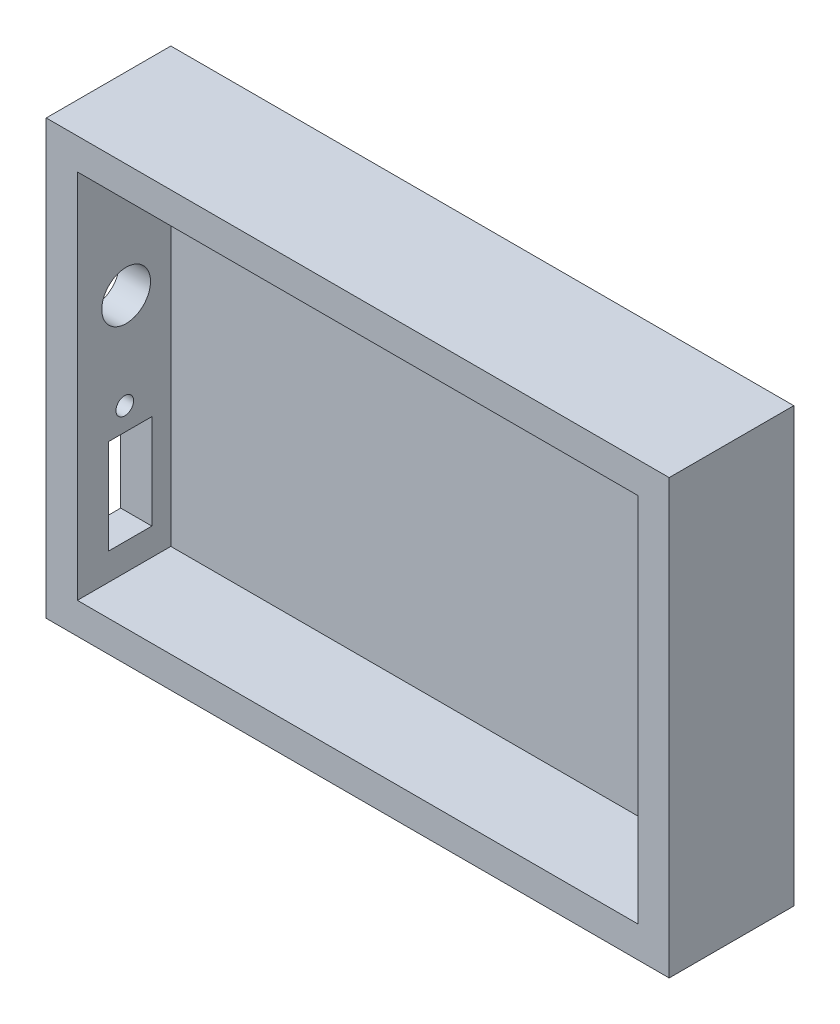
SolidWorks part; units mm, degrees
ref_plane "Front Plane" through (0, 0, 0) normal (0, 0, 1) x (1, 0, 0)
ref_plane "Top Plane" through (0, 0, 0) normal (0, 1, 0) x (1, 0, 0)
ref_plane "Right Plane" through (0, 0, 0) normal (1, 0, 0) x (0, 0, -1)
sketch "Sketch1" plane through (0, 0, 0) normal (0, 0, 1) x (1, 0, 0)
  line L1 (-115, 80) -> (115, 80)
  line L2 (-115, 80) -> (-115, -80)
  line L3 (-115, -80) -> (115, -80)
  line L4 (115, 80) -> (115, -80)
  line L5 (-115, 80) -> (115, -80) construction
  line L6 (-115, -80) -> (115, 80) construction
  point P0 (0, 0)
  dimension "D1" = 230
  dimension "D2" = 160
extrude "Boss-Extrude1" add sketch "Sketch1" along normal blind 46
shell "Shell1" thickness 11.5
sketch "Sketch2" plane through (-115, 0, 0) normal (-1, 0, 0) x (0, 0, 1)
  line L1 (34.5, -23.5) -> (18.5, -23.5)
  line L2 (34.5, -23.5) -> (34.5, -58.5)
  line L3 (34.5, -58.5) -> (18.5, -58.5)
  line L4 (18.5, -23.5) -> (18.5, -58.5)
  line L5 (34.5, -23.5) -> (18.5, -58.5) construction
  line L6 (34.5, -58.5) -> (18.5, -23.5) construction
  line L7 (46, -80) -> (0, -80) construction
  line L9 (46, 80) -> (0, 80) construction
  line L10 (46, 80) -> (46, -80) construction
  circle A0 centre (28.5, -15) radius 3.25
  circle A1 centre (28, 20) radius 9
  point P0 (26.5, -41)
  dimension "D4" = 8.5
  dimension "D6" = 6.5
  dimension "D7" = 18
  dimension "D1" = 56.5
  dimension "D2" = 35
  dimension "D3" = 17.5
  dimension "D5" = 16
  dimension "D8" = 60
  dimension "D9" = 18
  dimension "D10" = 11.5
extrude "Cut-Extrude1" cut sketch "Sketch2" against normal up to surface (11.5 mm away) up to face at (-103.5, 0, 28.75)
